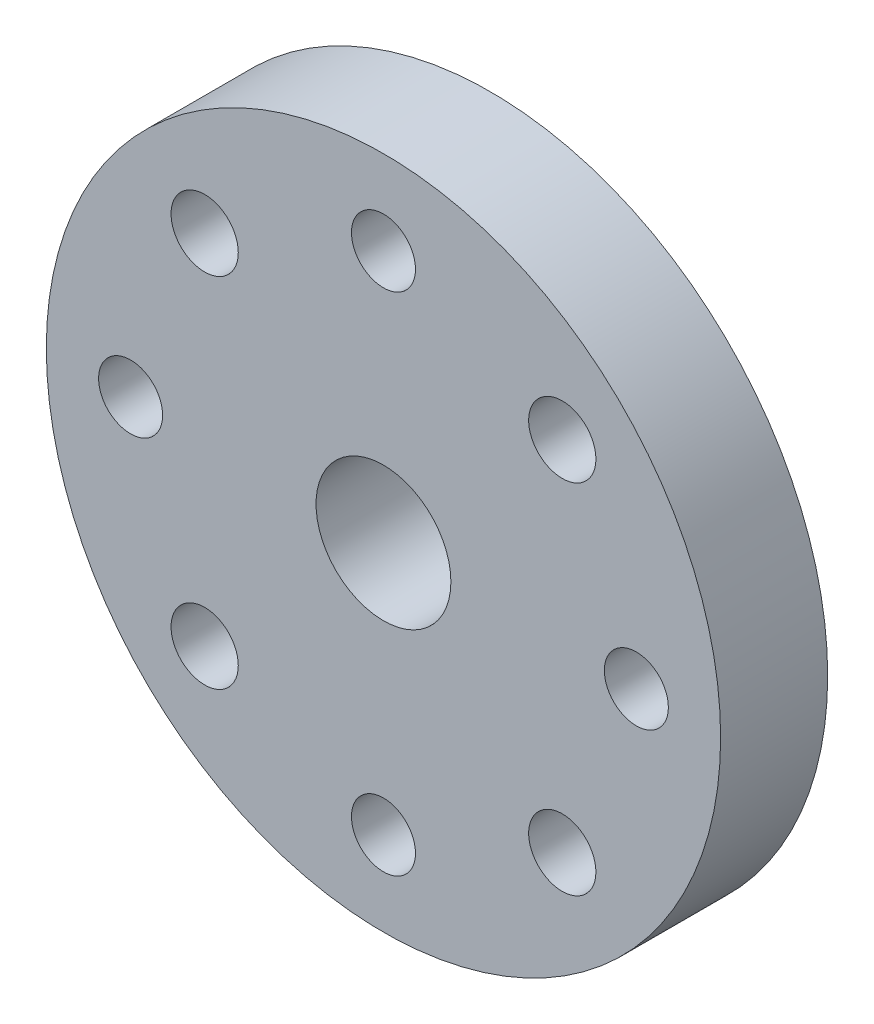
SolidWorks part; units mm, degrees
material "Balsa"
ref_plane "Front Plane" through (0, 0, 0) normal (0, 0, 1) x (1, 0, 0)
ref_plane "Top Plane" through (0, 0, 0) normal (0, 1, 0) x (1, 0, 0)
ref_plane "Right Plane" through (0, 0, 0) normal (1, 0, 0) x (0, 0, -1)
sketch "Sketch1" plane through (0, 0, 0) normal (0, 0, 1) x (1, 0, 0)
  circle A0 centre (0, 0) radius 20
  circle A1 centre (0, 0) radius 4
  circle A2 centre (0, 0) radius 15 construction
  circle A3 centre (0, 15) radius 1.8986
  circle A4 centre (10.6066, 10.6066) radius 1.9939
  circle A5 centre (15, 0) radius 1.8986
  circle A6 centre (10.6066, -10.6066) radius 1.9939
  circle A7 centre (0, -15) radius 1.8986
  circle A8 centre (-10.6066, -10.6066) radius 1.9939
  circle A9 centre (-15, 0) radius 1.8986
  circle A10 centre (-10.6066, 10.6066) radius 1.9939
  dimension "D1" = 40
  dimension "D2" = 8
  dimension "D3" = 30
  dimension "D4" = 3.7973
  dimension "D5" = 3.9878
  dimension "D6" = 45
  dimension "D7" = 4
extrude "Boss-Extrude1" add sketch "Sketch1" along normal blind 6.35
other "Move Face2" [suppressed] parameters "D1"=0.08
